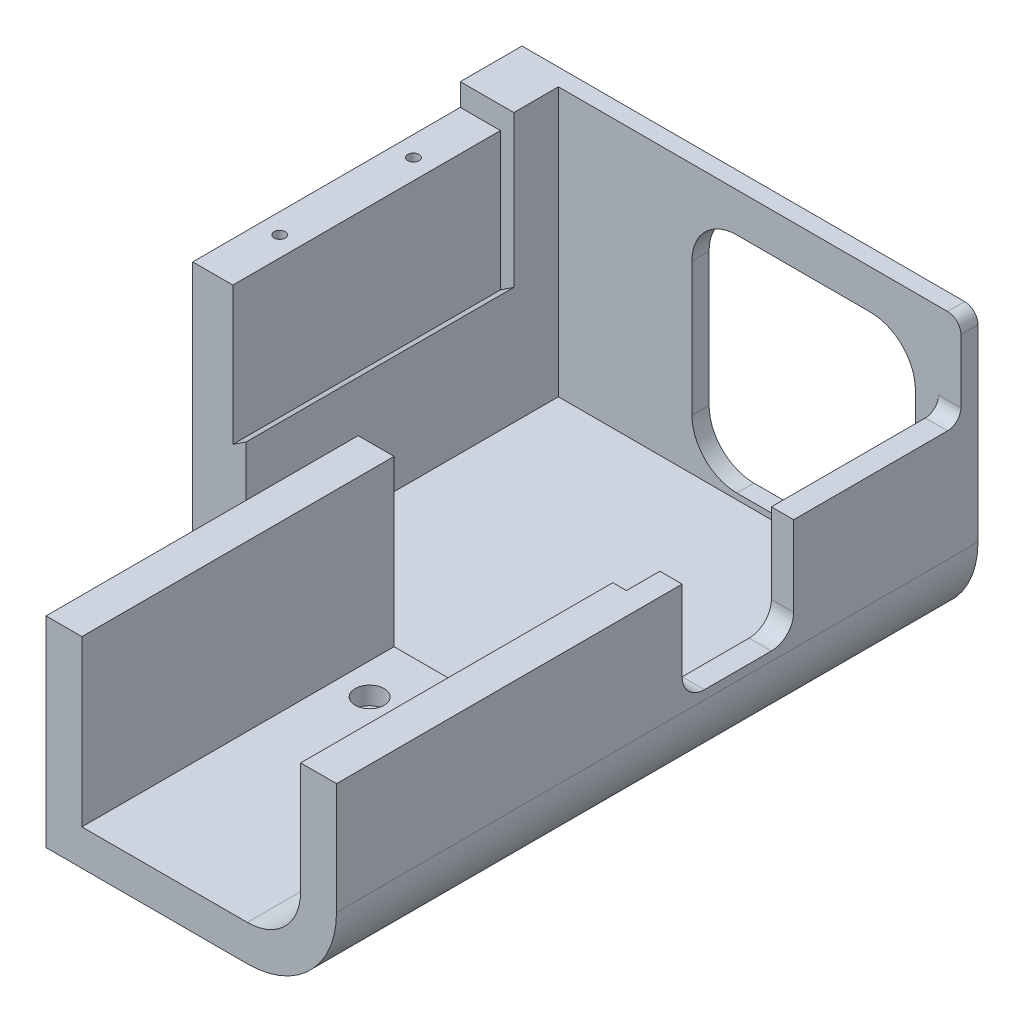
SolidWorks part; units mm, degrees
material "6061 Alloy"
ref_plane "Front Plane" through (0, 0, 0) normal (0, 0, 1) x (1, 0, 0)
ref_plane "Top Plane" through (0, 0, 0) normal (0, 1, 0) x (1, 0, 0)
ref_plane "Right Plane" through (0, 0, 0) normal (1, 0, 0) x (0, 0, -1)
sketch "Sketch2" plane through (0, 0, 0) normal (0, 0, 1) x (1, 0, 0)
  line L0 (85.25, 15) -> (85.25, 45.2)
  line L1 (70.25, 60.2) -> (0, 60.2)
  line L2 (0, 60.2) -> (0, 33.96)
  line L3 (0, 33.96) -> (-3, 35.94)
  line L4 (-3, 35.94) -> (-3, 24.26)
  line L6 (-3, 24.26) -> (0, 26.24)
  line L7 (0, 26.24) -> (0, 0)
  line L8 (0, 0) -> (70.25, 0)
  line L9 (30, 41.37) -> (30, 11.37)
  line L10 (40, 1.37) -> (70, 1.37)
  line L11 (80, 11.37) -> (80, 41.37)
  line L12 (70, 51.37) -> (40, 51.37)
  arc A0 (70.25, 0) -> (85.25, 15) centre (70.25, 15) ccw
  arc A1 (85.25, 45.2) -> (70.25, 60.2) centre (70.25, 45.2) ccw
  arc A2 (30, 11.37) -> (40, 1.37) centre (40, 11.37) ccw
  arc A3 (70, 1.37) -> (80, 11.37) centre (70, 11.37) ccw
  arc A4 (80, 41.37) -> (70, 51.37) centre (70, 41.37) ccw
  arc A5 (40, 51.37) -> (30, 41.37) centre (40, 41.37) ccw
  dimension "D3" = 15
  dimension "D4" = 3
  dimension "D7" = 10
  dimension "D1" = 85.25
  dimension "D2" = 60.2
  dimension "D5" = 11.68
  dimension "D6" = 7.72
  dimension "D8" = 50
  dimension "D9" = 50
  dimension "D10" = 5.25
  dimension "D11" = 1.37
ref_plane "Plane1" through (0, 0, 70) normal (0, 0, 1) x (1, 0, 0)
sketch "Sketch4" plane through (0, 0, 70) normal (0, 0, 1) x (1, 0, 0)
  line L0 (82.2, 15) -> (82.2, 45.2)
  line L1 (70.25, 57.15) -> (33.15, 57.15)
  line L2 (33.15, 57.15) -> (33.15, 3.05)
  line L3 (33.15, 3.05) -> (70.25, 3.05)
  line L4 (85.25, 15) -> (85.25, 45.2) construction
  line L5 (0, 0) -> (70.25, 0) construction
  arc A0 (82.2, 45.2) -> (70.25, 57.15) centre (70.25, 45.2) ccw
  arc A1 (70.25, 3.05) -> (82.2, 15) centre (70.25, 15) ccw
  dimension "D3" = 11.95
  dimension "D1" = 54.1
  dimension "D2" = 49.05
  dimension "D4" = 3.05
  dimension "D5" = 3.05
sketch "Sketch3" plane through (0, 0, 0) normal (0, 0, 1) x (1, 0, 0)
  line L0 (85.25, 15) -> (85.25, 45.2) construction
  line L1 (0, 0) -> (70.25, 0) construction
  line L2 (0, 26.24) -> (0, 0) construction
  line L5 (85.25, 15) -> (85.25, 40)
  line L6 (0, 0) -> (70.25, 0)
  line L7 (0, 60.2) -> (0, 0)
  line L10 (0, 60.2) -> (-12, 60.2)
  line L11 (-12, -5) -> (70.25, -5)
  line L12 (90.25, 15) -> (90.25, 40)
  line L13 (0, -5) -> (70.25, -5) construction
  line L14 (-12, 60.2) -> (-12, -5)
  line L15 (85.25, 40) -> (90.25, 40)
  arc A0 (70.25, 0) -> (85.25, 15) centre (70.25, 15) ccw construction
  arc A1 (70.25, 0) -> (85.25, 15) centre (70.25, 15) ccw
  arc A2 (70.25, -5) -> (90.25, 15) centre (70.25, 15) ccw
  dimension "D1" = 5
  dimension "D2" = 40
  dimension "D3" = 12
extrude "Boss-Extrude1" add sketch "Sketch3" along normal up to surface (70 mm away) up to plane "Plane1"
sketch "Sketch5" plane through (0, 0, 70) normal (0, 0, 1) x (1, 0, 0)
  line L0 (82.2, 15) -> (82.2, 45.2) construction
  line L1 (33.15, 3.05) -> (70.25, 3.05) construction
  line L2 (33.15, 57.15) -> (33.15, 3.05) construction
  line L3 (82.2, 15) -> (82.2, 40)
  line L4 (33.15, 3.05) -> (70.25, 3.05)
  line L5 (33.15, 40) -> (33.15, 3.05)
  line L6 (25.1, 40) -> (25.1, -5)
  line L7 (25.1, -5) -> (70.25, -5)
  line L8 (90.25, 15) -> (90.25, 40)
  line L9 (33.15, 57.15) -> (33.15, 3.05) construction
  line L10 (25.1, 57.15) -> (25.1, -5) construction
  line L11 (25.1, 40) -> (33.15, 40)
  line L12 (82.2, 40) -> (90.25, 40)
  arc A0 (70.25, 3.05) -> (82.2, 15) centre (70.25, 15) ccw construction
  arc A1 (70.25, 3.05) -> (82.2, 15) centre (70.25, 15) ccw
  arc A2 (70.25, -5) -> (90.25, 15) centre (70.25, 15) ccw
  dimension "D1" = 8.05
extrude "Boss-Extrude2" add sketch "Sketch5" along normal blind 70
sketch "Sketch6" plane through (0, 0, 70) normal (0, 0, 1) x (1, 0, 0)
  line L0 (-3, 24.26) -> (0, 26.24) construction
  line L1 (-3, 35.94) -> (-3, 24.26) construction
  line L2 (-3, 24.26) -> (0, 26.24)
  line L3 (-3, 60.2) -> (-3, 24.26)
  line L4 (0, 60.2) -> (-12, 60.2) construction
  line L5 (0, 26.24) -> (0, 60.2)
  line L6 (0, 60.2) -> (-3, 60.2)
extrude "Cut-Extrude1" cut sketch "Sketch6" against normal offset from surface (60 mm away) 10 up to face at (47.4749, 21.3151, 0)
sketch "Sketch13" plane through (0, 60.2, 0) normal (0, 1, 0) x (1, 0, 0)
  line L0 (-35.86, -70) -> (35.86, -70) construction
  line L1 (-3, -10) -> (-12, -10)
  line L2 (-3, -10) -> (-3, -70)
  line L3 (-3, -70) -> (-12, -70)
  line L4 (-12, -10) -> (-12, -70)
  line L5 (-12, -70) -> (-12, 0) construction
extrude "Cut-Extrude3" cut sketch "Sketch13" against normal blind 5
sketch "Sketch12" plane through (90.25, 0, 0) normal (1, 0, 0) x (0, 0, -1)
  line L0 (-70, 35.86) -> (-70, -35.86) construction
  line L2 (-62.5, 17) -> (-37.5, 17)
  line L3 (-62.5, 17) -> (-62.5, 40)
  line L4 (-62.5, 40) -> (-37.5, 40)
  line L5 (-37.5, 17) -> (-37.5, 40)
  line L9 (0, 15) -> (0, 45.2) construction
  line L10 (-140, 40) -> (0, 40) construction
  circle A0 centre (-50, 30.1) radius 7.5 construction
  point P13 (0, 30.1)
  point P17 (-50, 40)
  dimension "D1" = 15
  dimension "D2" = 20
  dimension "D3" = 25
  dimension "D4" = 23
extrude "Cut-Extrude2" cut sketch "Sketch12" against normal up to surface (5 mm away) up to face at (85.25, 27.5, 35)
sketch "Sketch7" plane through (0, 0, 0) normal (0, 0, 1) x (1, 0, 0)
  line L0 (70, 51.37) -> (40, 51.37) construction
  line L1 (30, 41.37) -> (30, 11.37) construction
  line L2 (40, 1.37) -> (70, 1.37) construction
  line L3 (80, 11.37) -> (80, 41.37) construction
  line L4 (70, 51.37) -> (40, 51.37)
  line L5 (30, 41.37) -> (30, 11.37)
  line L6 (40, 1.37) -> (70, 1.37)
  line L7 (80, 11.37) -> (80, 41.37)
  line L8 (-12, 60.2) -> (-12, -5) construction
  line L9 (-12, -5) -> (70.25, -5) construction
  line L10 (90.25, 15) -> (90.25, 40) construction
  line L11 (-12, 60.2) -> (-12, -5)
  line L12 (-12, -5) -> (70.25, -5)
  line L13 (90.25, 15) -> (90.25, 60.2)
  line L14 (0, 60.2) -> (-12, 60.2) construction
  line L15 (90.25, 60.2) -> (-12, 60.2)
  arc A0 (80, 41.37) -> (70, 51.37) centre (70, 41.37) ccw construction
  arc A1 (40, 51.37) -> (30, 41.37) centre (40, 41.37) ccw construction
  arc A2 (30, 11.37) -> (40, 1.37) centre (40, 11.37) ccw construction
  arc A3 (70, 1.37) -> (80, 11.37) centre (70, 11.37) ccw construction
  arc A4 (80, 41.37) -> (70, 51.37) centre (70, 41.37) ccw
  arc A5 (40, 51.37) -> (30, 41.37) centre (40, 41.37) ccw
  arc A6 (30, 11.37) -> (40, 1.37) centre (40, 11.37) ccw
  arc A7 (70, 1.37) -> (80, 11.37) centre (70, 11.37) ccw
  arc A8 (70.25, -5) -> (90.25, 15) centre (70.25, 15) ccw construction
  arc A9 (70.25, -5) -> (90.25, 15) centre (70.25, 15) ccw
extrude "Boss-Extrude3" add sketch "Sketch7" against normal blind 3.84
hole_wizard "CBORE for M3 SHCS1" positions "Sketch10" profile "Sketch11" counterbore size "M3" standard "ANSI Metric"
sketch "Sketch10" plane through (0, 3.05, 0) normal (0, 1, 0) x (1, 0, 0)
  line L1 (25.1, -70) -> (70.25, -70) construction
  line L2 (25.1, -70) -> (25.1, -95) construction
  line L3 (25.1, -95) -> (70.25, -95) construction
  line L4 (70.25, -70) -> (70.25, -95) construction
  line L5 (40.175, -82.5) -> (55.175, -82.5) construction
  line L8 (70.25, -140) -> (70.25, -70) construction
  point P0 (40.175, -82.5)
  point P2 (55.175, -82.5)
  point P58 (25.1, -82.5)
  point P59 (47.675, -82.5)
  point P60 (47.675, -95)
  dimension "D1" = 15
  dimension "D2" = 45.15
  dimension "D3" = 25
sketch "Sketch11" plane through (40.175, 3.05, 82.5) normal (1, 0, 0) x (0, 0, 1)
  line L0 (0, 0) -> (0, 9.0715)
  line L1 (0, 9.0715) -> (1.7, 8.05)
  line L2 (1.7, 8.05) -> (1.7, 4)
  line L3 (1.7, 4) -> (3.25, 4)
  line L4 (3.25, 4) -> (3.25, 0)
  line L5 (3.25, 0) -> (0, 0)
  line L10 (0, 9.0715) -> (-1.7, 8.05) construction
  line L11 (0, -6.35) -> (0, 107.95) construction
  dimension "Hole Dia." = 3.4
  dimension "Hole Depth" = 8.05
  dimension "C'Bore Dia." = 6.5
  dimension "C'Bore Depth" = 4
  dimension "Drill Angle" = 118
hole_wizard "M3x0.5 Tapped Hole1" positions "Sketch14" profile "Sketch15" tap size "M3x0.5" standard "ANSI Metric"
sketch "Sketch14" plane through (0, 55.2, 0) normal (0, 1, 0) x (1, 0, 0)
  line L0 (-7.5, -25) -> (-7.5, -55) construction
  line L2 (-12, -10) -> (-12, -70) construction
  line L3 (-3, -10) -> (-12, -10) construction
  point P0 (-7.5, -25)
  point P2 (-7.5, -55)
  point P11 (-12, -40)
  point P12 (-7.5, -40)
  point P15 (-7.5, -10)
  dimension "D1" = 30
sketch "Sketch15" plane through (-7.5, 55.2, 25) normal (1, 0, 0) x (0, 0, 1)
  line L0 (0, 0) -> (0, 14.7511)
  line L1 (0, 14.7511) -> (1.25, 14)
  line L2 (1.25, 14) -> (1.25, 0)
  line L5 (1.25, 0) -> (0, 0)
  line L10 (0, 14.7511) -> (-1.25, 14) construction
  line L11 (0, -6.35) -> (0, 107.95) construction
  dimension "Tap Drill Dia." = 2.5
  dimension "Tap Drill Depth" = 14
  dimension "Drill Angle" = 118
cosmetic thread "Hole Thread1" parameters "D1"=6, "D2"=3
cosmetic thread "Hole Thread2" parameters "D1"=6, "D2"=3
fillet "Fillet1" radius 10 1 edges at (25.1, -2.5, 70)
fillet "Fillet4" radius 5 2 edges at (87.75, 17, 37.5) (87.75, 17, 62.5)
fillet "Fillet5" radius 3 2 edges at (90.25, 60.2, -1.92) (87.75, 40, 0)
other "Tolerance" face at (33.9645, 5.3345, -1.92) face at (30, 26.37, -1.92) face at (33.9645, 47.4055, -1.92) face at (55, 51.37, -1.92) face at (76.0355, 47.4055, -1.92) face at (80, 26.37, -1.92) face at (76.0355, 5.3345, -1.92) face at (55, 1.37, -1.92) parameters "D1"=0.05
